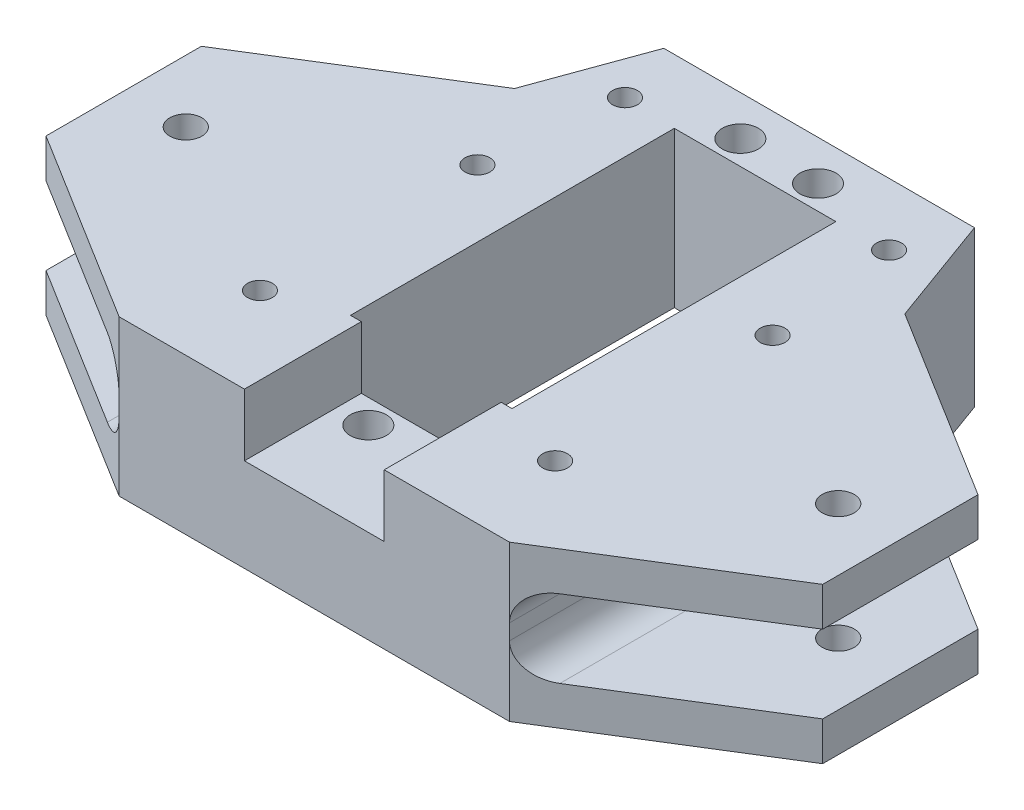
SolidWorks part; units mm, degrees
ref_plane "Front Plane" through (0, 0, 0) normal (0, 0, 1) x (1, 0, 0)
ref_plane "Top Plane" through (0, 0, 0) normal (0, 1, 0) x (1, 0, 0)
ref_plane "Right Plane" through (0, 0, 0) normal (1, 0, 0) x (0, 0, -1)
sketch "Sketch1" plane through (0, 0, 0) normal (0, 1, 0) x (1, 0, 0)
  line L0 (0, 0) -> (0, 55585.7092) construction
  line L1 (0, 0) -> (55585.7092, 0) construction
  line L2 (20, 39.5477) -> (-20, 39.5477)
  line L3 (-20, 39.5477) -> (-25.1303, 25.4523)
  line L4 (-25.1303, 25.4523) -> (-50, 10)
  line L5 (-50, 10) -> (-50, -10)
  line L11 (50, 10) -> (50, -10)
  line L12 (25.1303, 25.4523) -> (50, 10)
  line L13 (20, 39.5477) -> (25.1303, 25.4523)
  line L14 (25.1303, -25.4523) -> (50, -10)
  line L15 (-25.1303, -25.4523) -> (-50, -10)
  line L19 (25.1303, -25.4523) -> (-25.1303, -25.4523)
  point P7 (50, 0)
  point P12 (-50, 0)
  point P14 (0, -10.7407)
  point P19 (0, 39.5477)
  dimension "D1" = 40
  dimension "D2" = 20
  dimension "D3" = 65
  dimension "D4" = 100
  dimension "D5" = 110
  dimension "D8" = 15
extrude "Main-Body" add sketch "Sketch1" along normal mid plane 20
sketch "Sketch2" plane through (0, 10, 0) normal (0, 1, 0) x (1, 0, 0)
  line L0 (0, 47.5477) -> (0, -49952.4523) construction
  line L1 (-50, 0) -> (49950, 0) construction
  line L2 (20, 39.5477) -> (-20, 39.5477) construction
  line L3 (-10, 10.45) -> (10, 10.45) construction
  line L4 (10, -10) -> (-10, -10) construction
  line L5 (-10, -10) -> (-10, 30.9) construction
  line L6 (-10, 30.9) -> (10, 30.9) construction
  line L7 (10, -10) -> (10, 30.9) construction
  line L8 (0, -25.4523) -> (50000, -25.4523) construction
  line L9 (-50, 10) -> (-50, -10) construction
  line L10 (-5, 34.4) -> (5, 34.4) construction
  line L11 (-5, -13.5) -> (5, -13.5) construction
  line L12 (-25.1303, -25.4523) -> (25.1303, -25.4523) construction
  line L14 (-10.4, 31.3) -> (10.4, 31.3)
  line L15 (-10.4, 31.3) -> (-10.4, -10.4)
  line L16 (-10.4, -10.4) -> (10.4, -10.4)
  line L17 (10.4, 31.3) -> (10.4, -10.4)
  line L18 (-10.4, 31.3) -> (10.4, -10.4) construction
  line L19 (-10.4, -10.4) -> (10.4, 31.3) construction
  circle A0 centre (-5, -13.5) radius 2.325
  circle A1 centre (5, -13.5) radius 2.325
  circle A2 centre (-5, 34.4) radius 2.325
  circle A3 centre (5, 34.4) radius 2.325
  circle A4 centre (0, 0) radius 2 construction
  circle A5 centre (-42, 0) radius 2.0625
  circle A6 centre (42, 0) radius 2.0625
  point P22 (0, -10)
  point P23 (0, 30.9)
  point P28 (0, 39.5477)
  point P29 (0, -13.5)
  point P30 (0, 34.4)
  point P31 (-50, 0)
  point P32 (0, 10.45)
  dimension "D1" = 4.65
  dimension "D4" = 4.65
  dimension "D10" = 4.65
  dimension "D11" = 4.65
  dimension "D13" = 4
  dimension "D16" = 4.125
  dimension "D3" = 10
  dimension "D6" = 10
  dimension "D7" = 20
  dimension "D8" = 3.5
  dimension "D9" = 3.5
  dimension "D5" = 40.9
  dimension "D2" = 0.4
  dimension "D12" = 0.4
  dimension "D14" = 10
  dimension "D15" = 0
  dimension "D17" = 8
extrude "Servo&RotRod-Cutout" cut sketch "Sketch2" against normal blind 30
sketch "Sketch3" plane through (0, 0, 25.4523) normal (0, 0, 1) x (1, 0, 0)
  line L0 (0, 0) -> (0, 50000) construction
  line L1 (0, 0) -> (48695.3801, 0) construction
  line L3 (9, 10) -> (-9, 10)
  line L4 (-9, 10) -> (-9, 2)
  line L5 (-9, 2) -> (9, 2)
  line L6 (9, 10) -> (9, 2)
  line L7 (-25.1303, 10) -> (25.1303, 10) construction
  point P10 (0, 0)
  point P11 (0, 10)
  dimension "D1" = 18
  dimension "D2" = 8
  dimension "D3" = 0
extrude "Servo-Cable-Cutout" cut sketch "Sketch3" against normal up to surface (56.7523 mm away)
sketch "Sketch4" plane through (0, 0, 25.4523) normal (0, 0, 1) x (1, 0, 0)
  line L0 (0, 0) -> (0, 50000) construction
  line L1 (50, 0) -> (50050, 0) construction
  line L2 (50, 10) -> (50, -10) construction
  line L3 (-50, -5) -> (-50, 5)
  line L4 (-50, 10) -> (-50, -10) construction
  line L5 (-50, 5) -> (-25.1303, 5)
  line L6 (-25.1303, 5) -> (-25.1303, -5)
  line L7 (-50, -5) -> (-25.1303, -5)
  line L10 (-25.1303, 10) -> (-25.1303, -10) construction
  point P7 (50, 0)
  point P15 (-25.1303, 0)
  point P16 (-50, 0)
  dimension "D1" = 0
  dimension "D2" = 10
extrude "Control-Arm-Cutout" cut sketch "Sketch4" against normal through all both and the other way through all
mirror "Mirror1" about plane through (0, 0, 0) normal (1, 0, 0) of "Control-Arm-Cutout"
sketch "Sketch5" plane through (0, 10, 0) normal (0, 1, 0) x (1, 0, 0)
  line L0 (-50, 0) -> (49950, 0) construction
  line L1 (-50, 10) -> (-50, -10) construction
  line L2 (0, 0) -> (0, 50000) construction
  circle A0 centre (-40, 0) radius 2.05
  point P4 (-50, 0)
  dimension "D1" = 4.1
  dimension "D2" = 10
extrude "Cut-Extrude4" [suppressed] cut sketch "Sketch5" against normal through all both and the other way through all
mirror "Mirror2" [suppressed] about plane through (0, 0, 0) normal (1, 0, 0)
fillet "Fillet1" radius 4 4 edges at (-25.1303, -5, 0) (-25.1303, 5, 0) (25.1303, -5, 0) (25.1303, 5, 0)
sketch "Sketch6" plane through (0, -10, 0) normal (0, -1, 0) x (1, 0, 0)
  line L0 (0, 0) -> (0, -50000) construction
  line L1 (19, -12.4414) -> (19, -50012.4414) construction
  line L2 (-25.1303, 25.4523) -> (25.1303, 25.4523) construction
  line L3 (20, -39.5477) -> (-20, -39.5477) construction
  circle A0 centre (19, -14.5477) radius 1.6
  circle A1 centre (19, 13.4523) radius 1.6
  circle A2 centre (17, -31.5477) radius 1.6
  circle A3 centre (-17, -31.5477) radius 1.6
  circle A4 centre (-19, 13.4523) radius 1.6
  circle A5 centre (-19, -14.5477) radius 1.6
  dimension "D2" = 3.2
  dimension "D3" = 3.2
  dimension "D7" = 3.2
  dimension "D1" = 19
  dimension "D4" = 12
  dimension "D5" = 25
  dimension "D6" = 17
  dimension "D8" = 8
extrude "Mount-Holes-Chassis" cut sketch "Sketch6" against normal through all
sketch "Sketch7" plane through (0, -10, 0) normal (0, -1, 0) x (1, 0, 0)
  line L0 (0, 0) -> (0, -50000) construction
  circle A0 centre (17, -31.5477) radius 3.25
  circle A1 centre (19, -14.5477) radius 3.25
  circle A2 centre (19, 13.4523) radius 3.25
  circle A3 centre (-19, 13.4523) radius 3.25
  circle A4 centre (-19, -14.5477) radius 3.25
  circle A5 centre (-17, -31.5477) radius 3.25
  dimension "D1" = 6.5
  dimension "D2" = 6.5
  dimension "D3" = 6.5
extrude "Bolt-Head-Holes" cut sketch "Sketch7" against normal blind 8
equation "\"D10@Sketch2\"=\"D1@Sketch2\""
equation "\"D11@Sketch2\"=\"D1@Sketch2\""
equation "\"D3@Sketch6\"=\"D2@Sketch6\""
equation "\"D7@Sketch6\"=\"D2@Sketch6\""
equation "\"D2@Sketch7\"=\"D1@Sketch7\""
equation "\"D3@Sketch7\"=\"D1@Sketch7\""
